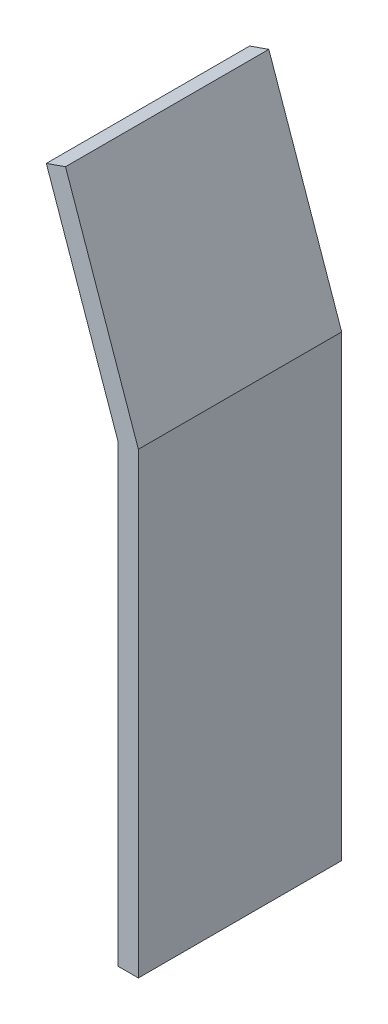
SolidWorks part; units mm, degrees
ref_plane "Front" through (0, 0, 0) normal (0, 0, 1) x (1, 0, 0)
ref_plane "Top" through (0, 0, 0) normal (0, 1, 0) x (1, 0, 0)
ref_plane "Right" through (0, 0, 0) normal (1, 0, 0) x (0, 0, -1)
sketch "Sketch1" plane through (0, 0, 0) normal (0, 0, 1) x (1, 0, 0)
  line L0 (0, 0) -> (0, -447)
  line L1 (0, -447) -> (20, -447)
  line L2 (20, -447) -> (20, 3.3971)
  line L4 (-51.669, 208.2808) -> (-70.5473, 201.6771)
  line L5 (-70.5473, 201.6771) -> (0, 0)
  line L6 (-51.669, 208.2808) -> (20, 3.3971)
  dimension "D1" = 20
  dimension "D2" = 20
  dimension "D3" = 447
  dimension "D4" = 213.66
  dimension "D5" = 160.72
  dimension "D6" = 217.0571
extrude "Boss-Extrude1" add sketch "Sketch1" along normal blind 200
